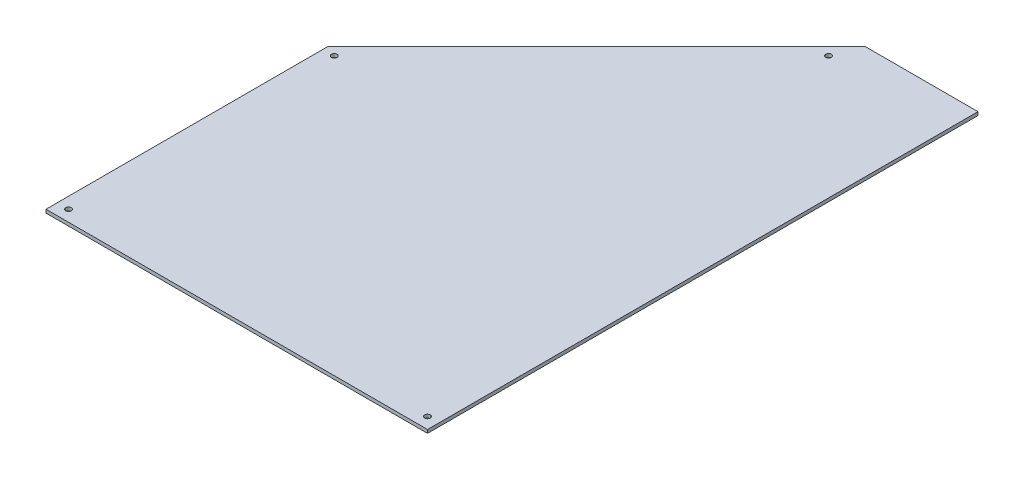
SolidWorks part; units mm, degrees
material "Acrylic (Medium-high impact)"
ref_plane "Front Plane" through (0, 0, 0) normal (0, 0, 1) x (1, 0, 0)
ref_plane "Top Plane" through (0, 0, 0) normal (0, 1, 0) x (1, 0, 0)
ref_plane "Right Plane" through (0, 0, 0) normal (1, 0, 0) x (0, 0, -1)
sketch "Sketch2" plane through (0, 0, 0) normal (0, 1, 0) x (1, 0, 0)
  line L0 (150, 250) -> (388.61, 488.61)
  line L1 (488.61, 588.61) -> (488.61, 0) construction
  line L2 (488.61, 0) -> (150, 0)
  line L3 (150, 0) -> (150, 250)
  line L4 (150, 250) -> (0, 100) construction
  line L5 (488.61, 488.61) -> (488.61, 0)
  line L6 (0, 0) -> (150, 0) construction
  line L7 (388.61, 488.61) -> (488.61, 588.61) construction
  line L9 (0, 100) -> (0, 0) construction
  line L10 (388.61, 488.61) -> (488.61, 488.61)
  dimension "D1" = 45
  dimension "D2" = 588.61
  dimension "D3" = 150
  dimension "D5" = 100
  dimension "D6" = 100
extrude "Boss-Extrude1" add sketch "Sketch2" along normal blind 3
sketch "Sketch3" plane through (0, 3, 0) normal (0, 1, 0) x (1, 0, 0)
  line L5 (478.61, 478.61) -> (392.7521, 478.61)
  line L6 (478.61, 478.61) -> (392.7521, 478.61) construction
  line L17 (478.61, 10) -> (478.61, 478.61)
  line L18 (392.7521, 478.61) -> (160, 245.8579)
  line L19 (160, 245.8579) -> (160, 10)
  line L20 (160, 10) -> (478.61, 10)
  line L21 (478.61, 10) -> (478.61, 478.61) construction
  line L22 (392.7521, 478.61) -> (160, 245.8579) construction
  line L23 (160, 245.8579) -> (160, 10) construction
  line L24 (160, 10) -> (478.61, 10) construction
  circle A1 centre (160, 245.8579) radius 2.5
  circle A2 centre (160, 10) radius 2.5
  circle A3 centre (478.61, 10) radius 2.5
  circle A4 centre (379.3689, 465.2267) radius 2.5
  dimension "D2" = 5
  dimension "D3" = 5
  dimension "D4" = 5
  dimension "D5" = 5
  dimension "D1" = 10
extrude "mounting-holes" cut sketch "Sketch3" against normal through all
